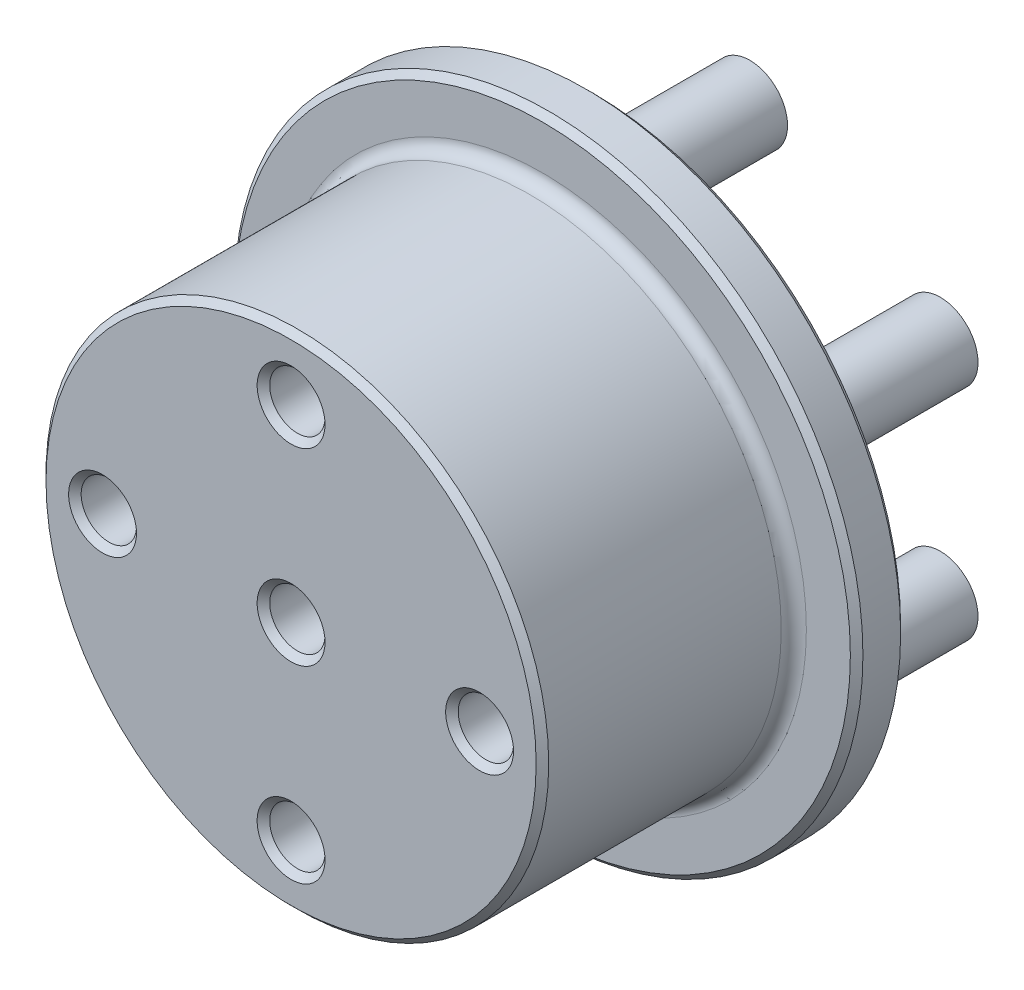
SolidWorks part; units mm, degrees
material "Polylactic Acid (PLA)"
ref_plane "Front Plane" through (0, 0, 0) normal (0, 0, 1) x (1, 0, 0)
ref_plane "Top Plane" through (0, 0, 0) normal (0, 1, 0) x (1, 0, 0)
ref_plane "Right Plane" through (0, 0, 0) normal (1, 0, 0) x (0, 0, -1)
sketch "Sketch1" plane through (0, 0, 0) normal (0, 0, 1) x (1, 0, 0)
  circle A0 centre (0, 0) radius 25
  circle A1 centre (0, 0) radius 15 construction
  dimension "D1" = 50
  dimension "D2" = 30
extrude "Boss-Extrude1" add sketch "Sketch1" against normal blind 4
sketch "Sketch2" plane through (0, 0, 0) normal (0, 0, 1) x (1, 0, 0)
  circle A0 centre (0, 0) radius 20
  dimension "D1" = 40
extrude "Boss-Extrude2" add sketch "Sketch2" along normal blind 20
fillet "Fillet1" radius 1 1 edges at (20, 0, 0)
sketch "Sketch3" plane through (0, 0, -4) normal (0, 0, -1) x (-1, 0, 0)
  circle A0 centre (0, 0) radius 10.2
  dimension "D1" = 20.4
extrude "Cut-Extrude1" cut sketch "Sketch3" against normal blind 5
sketch "Sketch4" plane through (0, 0, -4) normal (0, 0, -1) x (-1, 0, 0)
  circle A0 centre (0, 0) radius 17.5 construction
  circle A1 centre (0, 17.5) radius 3
  circle A2 centre (15.1554, 8.75) radius 3
  circle A3 centre (15.1554, -8.75) radius 3
  circle A4 centre (0, -17.5) radius 3
  circle A5 centre (-15.1554, -8.75) radius 3
  circle A6 centre (-15.1554, 8.75) radius 3
  circle A7 centre (0, 0) radius 10.2 construction
  point P17 (0, 0)
  dimension "D1" = 35
  dimension "D2" = 6
  dimension "D3" = 6
extrude "Boss-Extrude3" add sketch "Sketch4" along normal blind 12.5
sketch "Sketch7" plane through (0, 0, 20) normal (0, 0, 1) x (1, 0, 0)
  circle A0 centre (0, 0) radius 15 construction
  point P1 (0, 0)
  point P4 (0, 15)
  point P6 (15, 0)
  point P8 (0, -15)
  point P10 (-15, 0)
  dimension "D1" = 30
hole_wizard "Ø4.0mm Dowel Hole1" positions "Sketch7" profile "Sketch8" hole size "Ø4.0" standard "ISO"
sketch "Sketch8" plane through (0, 0, 20) normal (1, 0, 0) x (0, -1, 0)
  line L0 (0, 0) -> (0, 9.3219)
  line L1 (0, 9.3219) -> (2.2, 8)
  line L2 (2.2, 8) -> (2.2, 0)
  line L5 (2.2, 0) -> (0, 0)
  line L10 (0, 9.3219) -> (-2.2, 8) construction
  line L11 (0, -6.35) -> (0, 107.95) construction
  dimension "Hole Dia." = 4.4
  dimension "Hole Depth" = 8
  dimension "Drill Angle" = 118
fillet "Fillet2" radius 1 6 edges at (18.1554, 8.75, -4) (3, 17.5, -4) (-12.1554, 8.75, -4) (-12.1554, -8.75, -4) (3, -17.5, -4) (12.1554, -8.75, -4)
chamfer "Chamfer1" distance 0.5 angle 45 10 edges at (25, 0, -4) (-10.2, 0, -4) (-10.2, 0, 1) (25, 0, 0) (20, 0, 20) (-12.8, 0, 20) (2.2, -15, 20) (17.2, 0, 20) (2.2, 15, 20) (2.2, 0, 20)
